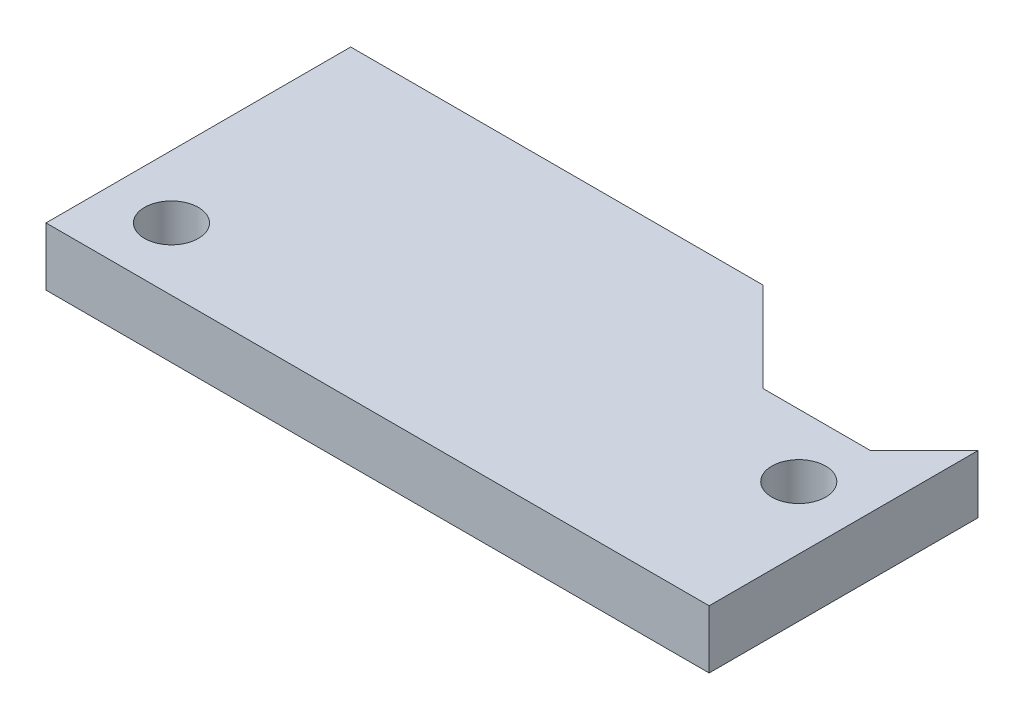
SolidWorks part; units mm, degrees
ref_plane "Front Plane" through (0, 0, 0) normal (0, 0, 1) x (1, 0, 0)
ref_plane "Top Plane" through (0, 0, 0) normal (0, 1, 0) x (1, 0, 0)
ref_plane "Right Plane" through (0, 0, 0) normal (1, 0, 0) x (0, 0, -1)
sketch "Sketch1" plane through (0, 0, 0) normal (0, 1, 0) x (1, 0, 0)
  line L0 (-18.5, 8.5) -> (18.5, -8.5) construction
  line L1 (-18.5, 8.5) -> (4.5, 8.5)
  line L2 (-18.5, 8.5) -> (-18.5, -8.5)
  line L3 (-18.5, -8.5) -> (18.5, -8.5)
  line L4 (18.5, 6.5) -> (18.5, -8.5)
  line L5 (4.5, 8.5) -> (9.5, 3.5)
  line L6 (9.5, 3.5) -> (15.5, 3.5)
  line L7 (15.5, 3.5) -> (18.5, 6.5)
  circle A0 centre (-15, -5) radius 1.5025
  circle A12 centre (15, 0) radius 1.5025
  arc A21 (9.3525, 3.6442) -> (10, 3.4975) centre (10, 5) ccw [skipped]
  arc A22 (15, 3.4975) -> (15.6475, 3.6442) centre (15, 5) ccw [skipped]
  circle A23 centre (-15, 0) radius 1.5025 [skipped]
  circle A24 centre (-15, 5) radius 1.5025 [skipped]
  circle A25 centre (-10, 0) radius 1.5025 [skipped]
  circle A26 centre (-10, -5) radius 1.5025 [skipped]
  circle A27 centre (-5, -5) radius 1.5025 [skipped]
  circle A28 centre (-5, 0) radius 1.5025 [skipped]
  arc A29 (-8.8302, 4.0571) -> (-11.4774, 5.2734) centre (-10, 5) ccw [skipped]
  circle A30 centre (-5, 5) radius 1.5025 [skipped]
  circle A31 centre (0, 5) radius 1.5025 [skipped]
  arc A32 (-1.3653, 0.6273) -> (1.3653, -0.6273) centre (0, 0) ccw [skipped]
  circle A33 centre (0, -5) radius 1.5025 [skipped]
  circle A34 centre (5, -5) radius 1.5025 [skipped]
  arc A35 (11.4774, -5.2734) -> (8.8302, -4.0571) centre (10, -5) ccw [skipped]
  circle A36 centre (10, 0) radius 1.5025 [skipped]
  circle A37 centre (5, 0) radius 1.5025 [skipped]
  circle A38 centre (5, 5) radius 1.5025 [skipped]
  circle A39 centre (15, -5) radius 1.5025 [skipped]
  dimension "D7" = 3.5
  dimension "D8" = 3.5
  dimension "D9" = 3.005
  dimension "D2" = 17
  dimension "D3" = 6
  dimension "D4" = 14
  dimension "D5" = 15
  dimension "D6" = 12
  dimension "D16" = 5
  dimension "D17" = 37
  dimension "D10" = 7
  dimension "D11" = 3
extrude "Boss-Extrude1" add sketch "Sketch1" along normal blind 3.25
